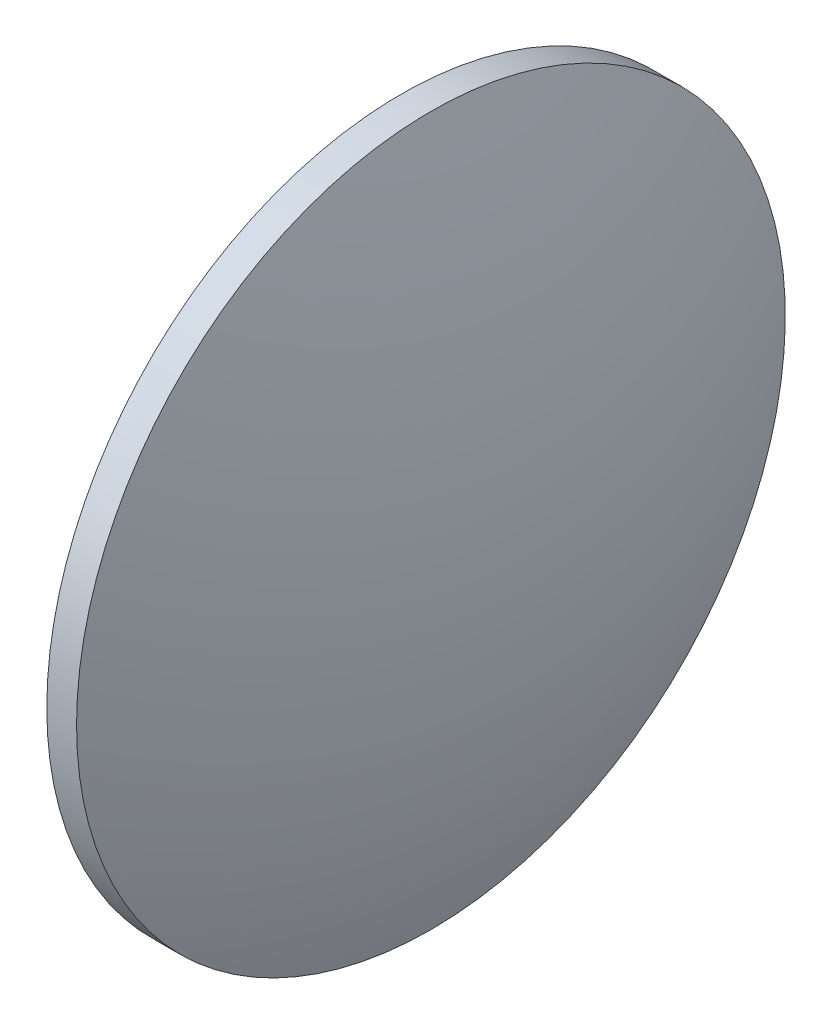
SolidWorks part; units mm, degrees
ref_plane "前视基准面" through (0, 0, 0) normal (0, 0, 1) x (1, 0, 0)
ref_plane "上视基准面" through (0, 0, 0) normal (0, 1, 0) x (1, 0, 0)
ref_plane "右视基准面" through (0, 0, 0) normal (1, 0, 0) x (0, 0, -1)
sketch "草图1" plane through (0, 0, 0) normal (0, 0, 1) x (1, 0, 0)
  line L0 (108.6656, 65.0209) -> (127.8417, 65.0209) construction
  line L1 (113.3138, 65.0209) -> (113.3138, 87.5209)
  line L2 (119.4138, 65.0209) -> (113.3138, 65.0209)
  line L5 (113.3138, 87.5209) -> (115.2038, 87.5209)
  arc A0 (119.4138, 65.0209) -> (115.2038, 87.5209) centre (57.1841, 65.0209) ccw
revolve "旋转1" add sketch "草图1" angle 360 about L0
